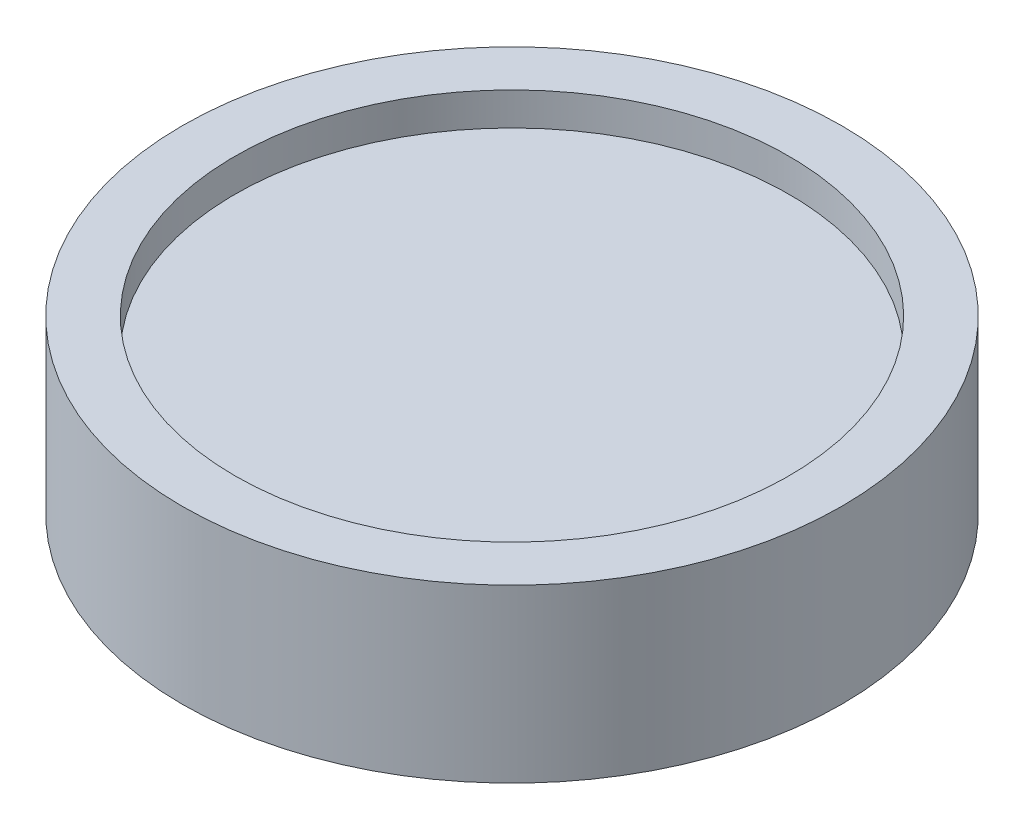
SolidWorks part; units mm, degrees
ref_plane "Front Plane" through (0, 0, 0) normal (0, 0, 1) x (1, 0, 0)
ref_plane "Top Plane" through (0, 0, 0) normal (0, 1, 0) x (1, 0, 0)
ref_plane "Right Plane" through (0, 0, 0) normal (1, 0, 0) x (0, 0, -1)
sketch "Sketch1" plane through (0, 0, 0) normal (0, 1, 0) x (1, 0, 0)
  circle A0 centre (0, 0) radius 50
  dimension "D1" = 100
extrude "Boss-Extrude1" add sketch "Sketch1" along normal blind 26
sketch "Sketch2" plane through (0, 26, 0) normal (0, 1, 0) x (1, 0, 0)
  circle A0 centre (0, 0) radius 42
extrude "Cut-Extrude1" cut sketch "Sketch2" against normal blind 5
sketch "Sketch3" plane through (0, 0, 0) normal (0, -1, 0) x (1, 0, 0)
  circle A0 centre (0, 0) radius 5
extrude "hub_distance_to_work_with" add sketch "Sketch3" along normal blind 10
